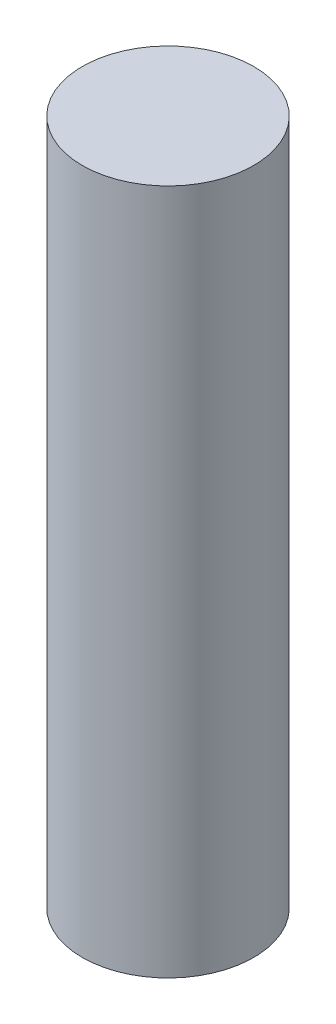
SolidWorks part; units mm, degrees
ref_plane "Front Plane" through (0, 0, 0) normal (0, 0, 1) x (1, 0, 0)
ref_plane "Top Plane" through (0, 0, 0) normal (0, 1, 0) x (1, 0, 0)
ref_plane "Right Plane" through (0, 0, 0) normal (1, 0, 0) x (0, 0, -1)
sketch "Sketch1" plane through (0, 0, 0) normal (0, 1, 0) x (1, 0, 0)
  circle A0 centre (0, 0) radius 10
  circle A1 centre (0, 0) radius 7.5
  dimension "D1" = 20
  dimension "D2" = 15
extrude "Boss-Extrude1" add sketch "Sketch1" along normal blind 80
sketch "Sketch2" plane through (0, 80, 0) normal (0, 1, 0) x (1, 0, 0)
  circle A0 centre (0, 0) radius 7.5
  circle A1 centre (0, 0) radius 7.5 construction
extrude "Boss-Extrude2" add sketch "Sketch2" against normal blind 5
